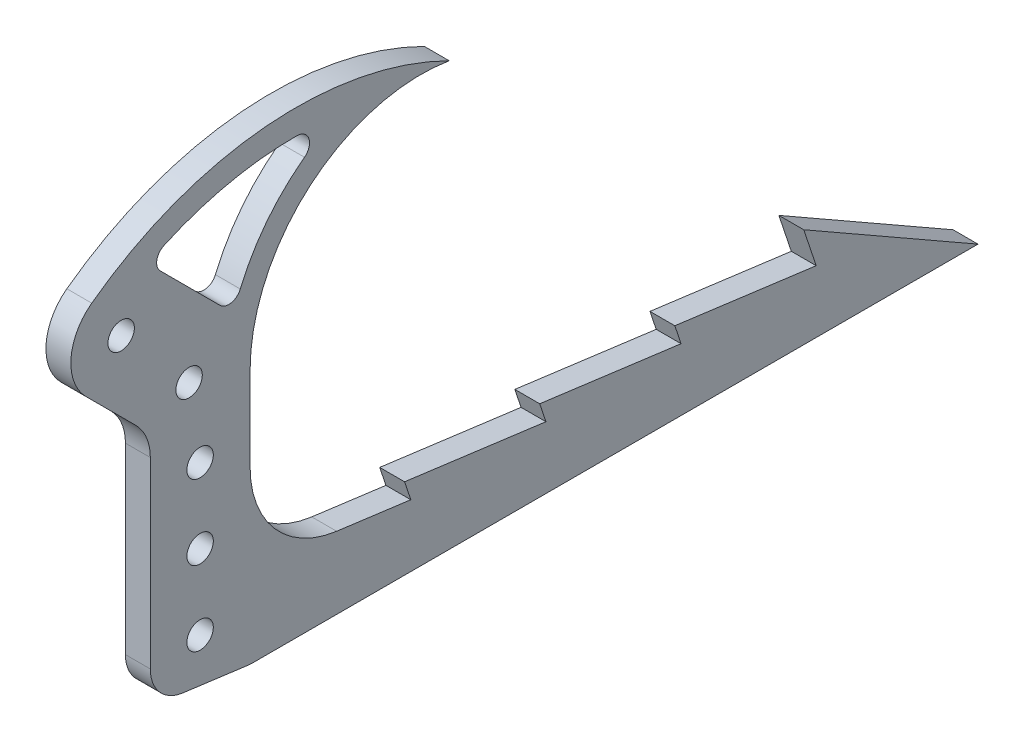
SolidWorks part; units mm, degrees
material "Plain Carbon Steel"
ref_plane "Front Plane" through (0, 0, 0) normal (0, 0, 1) x (1, 0, 0)
ref_plane "Top Plane" through (0, 0, 0) normal (0, 1, 0) x (1, 0, 0)
ref_plane "Right Plane" through (0, 0, 0) normal (1, 0, 0) x (0, 0, -1)
sketch "Sketch1" plane through (0, 0, 0) normal (1, 0, 0) x (0, 0, -1)
  line L0 (305.2991, -24.4357) -> (12.3959, 49.2644)
  line L2 (-10.6887, -49.6628) -> (281.6107, -75.2357)
  line L3 (281.6107, -75.2357) -> (339.725, -133.35)
  line L4 (339.725, -133.35) -> (339.725, -254)
  line L5 (339.725, -254) -> (390.6304, -254)
  line L6 (390.6304, -254) -> (390.6304, -109.767)
  line L7 (390.6304, -109.767) -> (305.2991, -24.4357)
  line L8 (281.6107, -75.2357) -> (305.2991, -24.4357) construction
  line L9 (339.725, -133.35) -> (390.6304, -109.767) construction
  circle A0 centre (0, 0) radius 19.05
  circle A1 centre (0, 0) radius 50.8
  dimension "D1" = 101.6
  dimension "D2" = 38.1
  dimension "D3" = 50.9054
  dimension "D4" = 135
  dimension "D5" = 135
  dimension "D6" = 254
  dimension "D7" = 339.725
  dimension "D8" = 120.65
  dimension "D9" = 50.8
  dimension "D10" = 110
  dimension "D11" = 110
extrude "Boss-Extrude1" add sketch "Sketch1" along normal blind 12.7
fillet "Fillet1" radius 25.4 2 edges at (6.35, -133.35, -339.725) (6.35, -75.2357, -281.6107)
fillet "Fillet2" radius 50.8 2 edges at (6.35, -109.767, -390.6304) (6.35, -24.4357, -305.2991)
hole_wizard "1/2 Clearance Hole1" positions "Sketch3" profile "Sketch2" hole size "1/2" standard "ANSI Inch"
sketch "Sketch3" plane through (12.7, 0, 0) normal (1, 0, 0) x (0, 0, -1)
  line L8 (306.1083, -63.8122) -> (350.246, -107.95)
  line L9 (365.125, -143.871) -> (365.125, -254)
  line L10 (306.1083, -63.8122) -> (350.246, -107.95)
  line L11 (365.125, -143.871) -> (365.125, -254)
  line L12 (339.725, -254) -> (390.6304, -254) construction
  arc A4 (365.125, -143.871) -> (350.246, -107.95) centre (314.325, -143.871) ccw
  arc A5 (365.125, -143.871) -> (350.246, -107.95) centre (314.325, -143.871) ccw
  point P34 (365.125, -234.95)
  point P36 (365.125, -196.85)
  point P38 (365.125, -158.75)
  point P40 (359.5071, -120.65)
  point P42 (324.846, -82.55)
  dimension "D2" = 38.1
  dimension "D3" = 19.05
  dimension "D4" = 38.1
  dimension "D5" = 38.1
  dimension "D6" = 38.1
  dimension "D1" = 25.4
sketch "Sketch2" plane through (12.7, -234.95, -365.125) normal (0, 1, 0) x (0, 0, -1)
  line L0 (0, 0) -> (0, 42.1535)
  line L1 (0, 42.1535) -> (6.7462, 38.1)
  line L2 (6.7462, 38.1) -> (6.7462, 0)
  line L5 (6.7462, 0) -> (0, 0)
  line L10 (0, 42.1535) -> (-6.7462, 38.1) construction
  line L11 (0, -6.35) -> (0, 107.95) construction
  dimension "Hole Dia." = 13.4925
  dimension "Hole Depth" = 38.1
  dimension "Drill Angle" = 118
sketch "Sketch4" plane through (12.7, 0, 0) normal (1, 0, 0) x (0, 0, -1)
  line L0 (288.1478, -81.7728) -> (332.2855, -125.9105) construction
  line L1 (375.7514, -94.888) -> (315.2192, -34.3558) construction
  line L2 (306.8855, -100.5105) -> (324.846, -82.55) construction
  line L3 (324.846, -82.55) -> (325.5076, -81.8884) construction
  line L4 (306.8855, -100.5105) -> (-73.7979, -100.5105)
  line L5 (-73.7979, -100.5105) -> (-73.7979, 83.4217)
  line L6 (-73.7979, 83.4217) -> (344.1297, 83.4217)
  line L7 (344.1297, 83.4217) -> (344.1297, -63.2663)
  line L8 (324.846, -82.55) -> (344.1297, -63.2663) construction
  circle A0 centre (325.5076, -81.8884) radius 26.3356
  circle M6 centre (0, 0) radius 19.05
  line M9 (375.7514, -94.888) -> (315.2192, -34.3558)
  arc M10 (315.2192, -34.3558) -> (291.694, -21.0124) centre (279.2982, -70.2768) ccw
  line M11 (291.694, -21.0124) -> (12.3959, 49.2644)
  arc M12 (12.3959, 49.2644) -> (-10.6887, -49.6628) centre (0, 0) ccw
  line M13 (-10.6887, -49.6628) -> (272.401, -74.4299)
  arc M14 (272.401, -74.4299) -> (288.1478, -81.7728) centre (270.1872, -99.7333) cw
  line M15 (288.1478, -81.7728) -> (332.2855, -125.9105)
extrude "Cut-Extrude1" cut sketch "Sketch4" against normal through all contours A0 M9 M10 M11 M12 M13 M14 M15 M6
sketch "Sketch5" plane through (12.7, 0, 0) normal (1, 0, 0) x (0, 0, -1)
  line L0 (243.118, -260.7234) -> (761.005, -260.7234) construction
  line L1 (339.725, -254) -> (390.6304, -260.7234)
  line L2 (390.6304, -260.7234) -> (762, -260.7234)
  line L3 (762, -260.7234) -> (673.1, -209.9234)
  line L4 (673.1, -209.9234) -> (679.45, -228.9734)
  line L5 (679.45, -228.9734) -> (607.333, -219.4484)
  line L6 (607.333, -219.4484) -> (610.508, -228.9734)
  line L7 (610.508, -228.9734) -> (538.3909, -219.4484)
  line L8 (538.3909, -219.4484) -> (541.5659, -228.9734)
  line L9 (541.5659, -228.9734) -> (469.4489, -219.4484)
  line L10 (469.4489, -219.4484) -> (472.6239, -228.9734)
  line L11 (472.6239, -228.9734) -> (400.5068, -219.4484)
  line L12 (607.333, -219.4484) -> (676.275, -219.4484) construction
  line L13 (400.5068, -219.4484) -> (390.6304, -218.144)
  line L14 (390.6304, -254) -> (390.6304, -130.809) construction
  line L15 (390.6304, -218.144) -> (390.6304, -254)
  line L16 (390.6304, -254) -> (339.725, -254)
  circle A1 centre (0, 0) radius 22.225 construction
  dimension "D1" = 762
  dimension "D2" = 31.75
  dimension "D3" = 88.9
  dimension "D4" = 82.55
  dimension "D5" = 50.8
extrude "Boss-Extrude2" add sketch "Sketch5" against normal up to surface (12.7 mm away) up to face at (0, -82.55, -331.5923)
fillet "Fillet3" radius 19.05 2 edges at (6.35, -260.7234, -390.6304) (6.35, -254, -339.725)
fillet "Fillet4" radius 50.8 1 edges at (6.35, -218.144, -390.6304)
sketch "Sketch6" plane through (12.7, 0, 0) normal (1, 0, 0) x (0, 0, -1)
  line L0 (390.6304, -173.6123) -> (390.6304, -130.809) construction
  line L1 (375.7514, -94.888) -> (344.1297, -63.2663)
  line L2 (344.1297, -63.2663) -> (309.8429, -60.7181)
  line L3 (390.6304, -130.809) -> (375.7514, -94.888)
  arc A0 (309.8429, -60.7181) -> (492.2304, -44.8234) centre (413.9961, -201.4771) cw
  arc A1 (344.1297, -63.2663) -> (306.8855, -100.5105) centre (325.5076, -81.8884) ccw construction
  arc A2 (492.2304, -44.8234) -> (390.6304, -130.809) centre (477.8159, -130.809) ccw
  dimension "D1" = 165.1
  dimension "D2" = 101.6
extrude "Boss-Extrude3" add sketch "Sketch6" against normal up to surface (12.7 mm away) up to face at (0, -82.55, -331.5923)
sketch "Sketch7" plane through (12.7, 0, 0) normal (1, 0, 0) x (0, 0, -1)
  line L7 (338.5344, -57.671) -> (375.7514, -94.888)
  line L10 (352.425, -143.871) -> (352.425, -237.3006)
  line L11 (377.9304, -173.6123) -> (377.9304, -130.809)
  line L12 (315.8658, -91.5303) -> (341.2658, -116.9303)
  arc A23 (375.7514, -94.888) -> (382.0215, -102.515) centre (339.8304, -130.809) cw
  arc A25 (352.425, -143.871) -> (341.2658, -116.9303) centre (314.325, -143.871) ccw
  arc A26 (317.397, -70.9272) -> (315.8658, -91.5303) centre (325.5076, -81.8884) ccw
  arc A27 (435.2105, -40.4659) -> (377.9304, -130.809) centre (477.8159, -130.809) ccw
  arc A28 (435.2105, -40.4659) -> (317.397, -70.9272) centre (413.9961, -201.4771) ccw
  arc A31 (435.2105, -40.4659) -> (382.0215, -102.515) centre (477.8159, -130.809) ccw
  arc A32 (435.2105, -40.4659) -> (338.5344, -57.671) centre (413.9961, -201.4771) ccw
  dimension "D1" = 12.7
extrude "Cut-Extrude2" cut sketch "Sketch7" against normal through all
fillet "Fillet7" radius 6.35 3 edges at (6.35, -102.515, -382.0215) (6.35, -40.4659, -435.2105) (6.35, -57.671, -338.5344)
